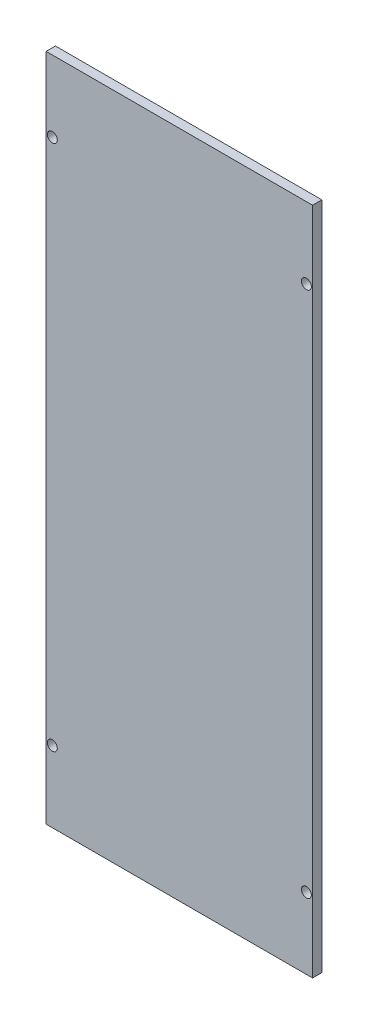
SolidWorks part; units mm, degrees
ref_plane "前视基准面" through (0, 0, 0) normal (0, 0, 1) x (1, 0, 0)
ref_plane "上视基准面" through (0, 0, 0) normal (0, 1, 0) x (1, 0, 0)
ref_plane "右视基准面" through (0, 0, 0) normal (1, 0, 0) x (0, 0, -1)
sketch "草图1" plane through (0, 0, 0) normal (0, 0, 1) x (1, 0, 0)
  line L1 (0, 0) -> (86, 0)
  line L2 (0, 0) -> (0, 216)
  line L3 (0, 216) -> (86, 216)
  line L4 (86, 0) -> (86, 216)
  dimension "D1" = 216
  dimension "D2" = 86
extrude "凸台-拉伸1" add sketch "草图1" along normal blind 3
sketch "草图2" plane through (0, 0, 3) normal (0, 0, 1) x (1, 0, 0)
  line L0 (0, 216) -> (0, 0) construction
  line L1 (43, 216) -> (43, 0) construction
  line L2 (86, 216) -> (0, 216) construction
  line L3 (0, 0) -> (86, 0) construction
  line L4 (43, 0) -> (43, 108) construction
  line L5 (43, 108) -> (119.7361, 108) construction
  circle A0 centre (2, 193) radius 1.6
  circle A1 centre (2, 23) radius 1.6
  circle A2 centre (84, 23) radius 1.6
  circle A3 centre (84, 193) radius 1.6
  point P6 (0, 0)
  dimension "D1" = 3.2
  dimension "D2" = 170
  dimension "D3" = 2
extrude "切除-拉伸1" cut sketch "草图2" against normal blind 3
